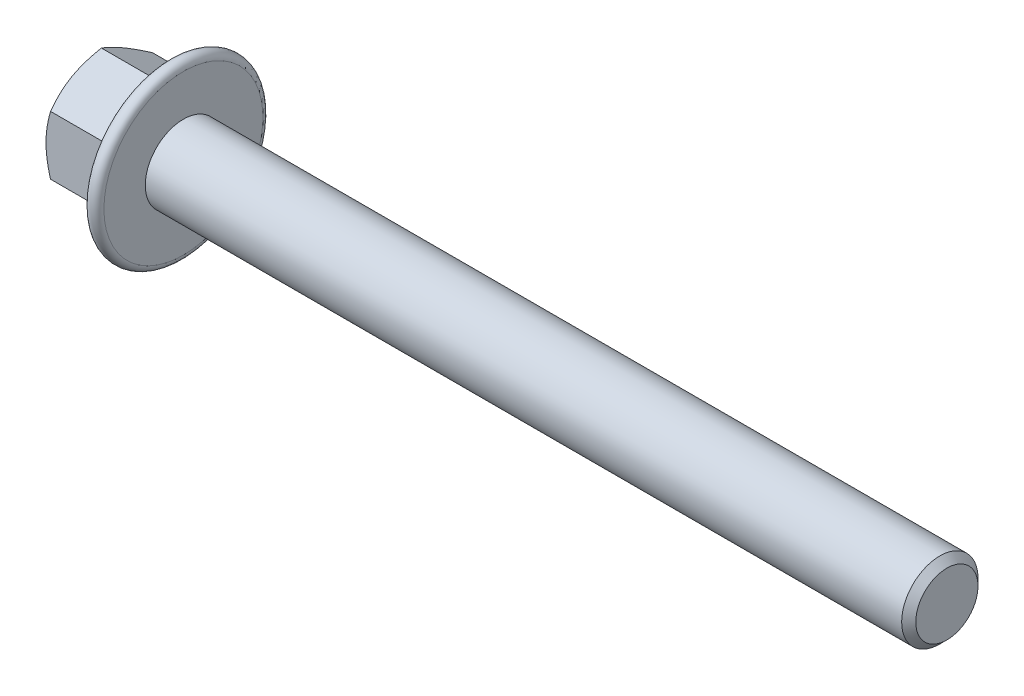
SolidWorks part; units mm, degrees
extrude "BaseHead" add sketch "Sketch1" along normal blind 6.8
sketch "Sketch1" plane through (0, 0, 0) normal (1, 0, 0) x (0, 0, -1)
  line L0 (4, 2.3094) -> (4, -2.3094)
  line L1 (-4, 2.3094) -> (-4, -2.3094)
  line L2 (4, -2.3094) -> (0, -4.6188)
  line L3 (0, -4.6188) -> (-4, -2.3094)
  line L4 (4, 2.3094) -> (0, 4.6188)
  line L5 (0, 4.6188) -> (-4, 2.3094)
ref_plane "Plane1" through (0, 0, 0) normal (0, 0, 1) x (1, 0, 0)
ref_plane "Plane2" through (0, 0, 0) normal (0, 1, 0) x (1, 0, 0)
ref_plane "Plane3" through (0, 0, 0) normal (1, 0, 0) x (0, 0, -1)
sketch "BodySke" plane through (0, 0, 0) normal (0, 0, 1) x (1, 0, 0)
  line L0 (0, 2.3094) -> (0, -2.3094) construction
  line L1 (0, 0) -> (66.8, 0)
  line L2 (0, 0) -> (0, 3)
  line L3 (0, 3) -> (66.2455, 3)
  line L4 (66.8, 0) -> (66.8, 2.4455)
  line L5 (6.8, 4.6188) -> (6.8, 2.3094) construction
  line L6 (66.8, 2.4455) -> (66.2455, 3)
  line L7 (0, 0) -> (96.52, 0) construction
  line L8 (66.8, -2.4455) -> (66.2455, -3) construction
  line L9 (0, -3) -> (66.2455, -3) construction
  line L10 (7.8, 15.24) -> (7.8, -1.27) construction
  line L11 (6.8, 15.24) -> (6.8, -1.27) construction
  line L12 (6.8, 2.3094) -> (6.8, -2.3094) construction
revolve "BaseBody" add sketch "BodySke"
cosmetic thread "ThreadCosmetic" [suppressed]
fillet "HeadFillet" [suppressed] radius 0.25
sketch "Sketch3" plane through (0, 0, 0) normal (0, 0, 1) x (1, 0, 0)
  line L0 (0, 4) -> (3.244, 9.6188)
  line L1 (0, 4.6188) -> (0, 2.3094) construction
  line L2 (3.244, 9.6188) -> (3.244, 14.6188)
  line L3 (3.244, 14.6188) -> (-10, 14.6188)
  line L4 (-10, 14.6188) -> (-10, 4)
  line L5 (-10, 4) -> (0, 4)
  line L6 (0, 0) -> (99.06, 0) construction
  line L7 (6.8, 4.6188) -> (0, 4.6188) construction
revolve "HeadChamfer" cut sketch "Sketch3" angle 360 about L6
sketch "Sketch4" plane through (0, 0, 0) normal (0, 0, 1) x (1, 0, 0)
  line L0 (3.3899, 0) -> (5.7332, 6.4381)
  line L1 (6.8, 4.6188) -> (6.8, 2.3094) construction
  line L2 (5.7, 34.3444) -> (5.7, 16.9779) construction
  line L3 (6.8, 0) -> (6.8, 6.25)
  line L4 (8.3021, 6.8) -> (20.1618, 6.8) construction
  line L5 (0, 0) -> (95.25, 0) construction
  line L6 (0, 0) -> (96.52, 0) construction
  line L7 (3.3899, 0) -> (6.8, 0)
  line L8 (8.3021, -6.8) -> (20.1618, -6.8) construction
  arc A0 (6.8, 6.25) -> (5.7332, 6.4381) centre (6.25, 6.25) ccw
  dimension "D1" = 20
  dimension "Flange_thickness" = 1.1
  dimension "Flange_dia" = 13.6
revolve "Flange" add sketch "Sketch4" angle 360 about L5
fillet "FlangeHexFillet" radius 0.11 6 edges
sketch "ThdSchSke" plane through (0, 0, 0) normal (0, 0, 1) x (1, 0, 0)
  line L0 (7.8, -2.4455) -> (7.4117, -3)
  line L1 (7.8, -2.4455) -> (8.1883, -3)
  line L2 (8.1883, -3) -> (8.1883, -3.75)
  line L3 (-3.175, 0) -> (5.1513, 0) construction
  line L5 (8.1883, -3.75) -> (7.4117, -3.75)
  line L6 (7.4117, -3.75) -> (7.4117, -3)
revolve "ThreadSchematic" [suppressed] cut sketch "ThdSchSke" angle 360 about L3
pattern_linear "ThdSchPat" [suppressed]
equation "\"D3@Sketch1\" = \"Width_flats@Sketch1\" / 2"
equation "\"D4@Sketch1\" = \"D3@Sketch1\""
equation "\"D5@Sketch1\" = \"D4@Sketch1\""
equation "\"Thread_minor@ThreadCosmetic\" = \"Minor_dia@BodySke\""
equation "\"D1@Sketch3\" = \"Width_flats@Sketch1\" / 2"
equation "\"Thread_length@ThreadCosmetic\" = ((sgn( (\"Length@BodySke\" - \"Advance@BodySke\" ) - \"Thread_nom@BodySke\" )-1)*( (\"Length@BodySke\" - \"Advance@BodySke\" ) - \"Thread_nom@BodySke\" ))/-2+ \"Thread_nom@BodySke\""
equation "\"Thread_minor@ThdSchSke\" = \"Minor_dia@BodySke\""
equation "\"Diameter@ThdSchSke\" = \"Diameter@BodySke\""
equation "\"Overcut@ThdSchSke\" = \"Diameter@BodySke\" * 1.25"
equation "\"Start@ThdSchSke\" = \"Head_ht@BaseHead\" + \"Length@BodySke\" - \"Thread_length@ThreadCosmetic\"  '---Non-countersunk---"
equation "\"Num_threads@ThdSchPat\" = int( \"Thread_length@ThreadCosmetic\" / \"Advance@BodySke\" + 0.999 )  + 1"
equation "\"Advance@ThdSchPat\" = \"Thread_length@ThreadCosmetic\" /  (\"Num_threads@ThdSchPat\" - 1) 'relax it"
equation "\"Num_threads@ThdSchPat\" = \"Num_threads@ThdSchPat\" - sgn( \"Num_threads@ThdSchPat\" - 1) '---chamfered tips only---"
